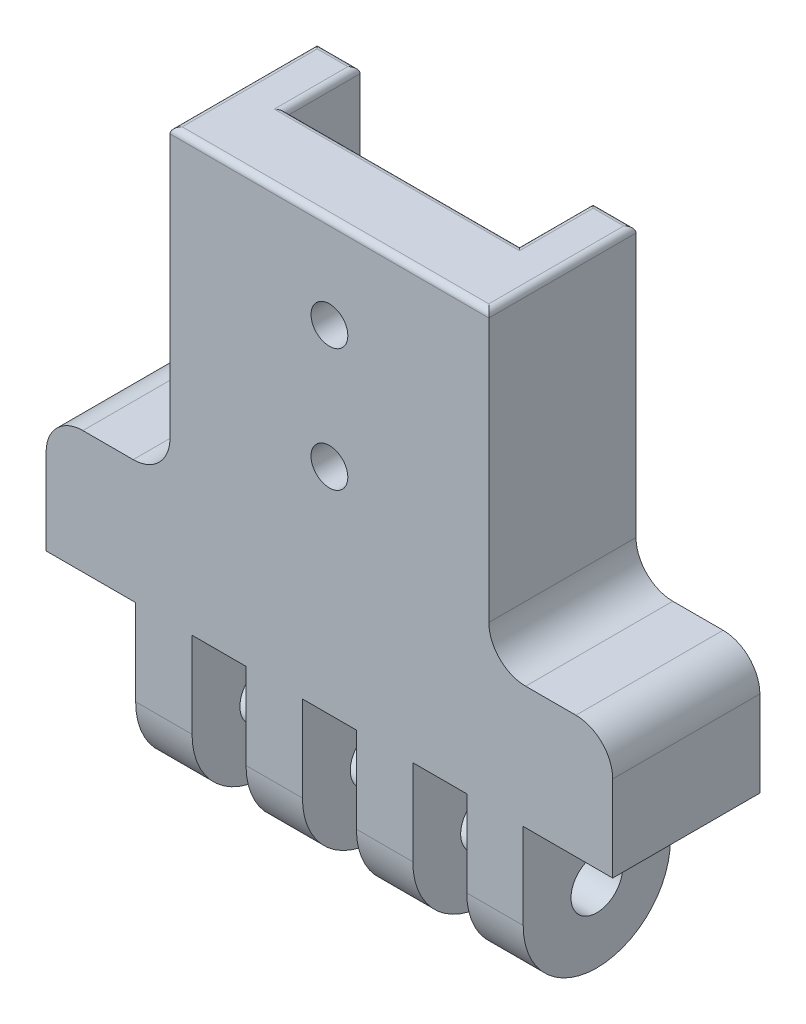
SolidWorks part; units mm, degrees
other "Markup1"
sketch "Sketch9" plane through (-23.1, -13, 8) normal (-0.4776, -0.6311, 0.6112) x (-0.7397, -0.0865, -0.6673)
sketch "Sketch13" plane through (-23.1, -13, 6) normal (-0.4776, -0.6311, 0.6112) x (-0.7397, -0.0865, -0.6673)
ref_plane "Front Plane" through (0, 0, 0) normal (0, 0, 1) x (1, 0, 0)
ref_plane "Top Plane" through (0, 0, 0) normal (0, 1, 0) x (1, 0, 0)
ref_plane "Right Plane" through (0, 0, 0) normal (1, 0, 0) x (0, 0, -1)
sketch "Sketch1" plane through (0, 0, 0) normal (0, 1, 0) x (1, 0, 0)
  line L1 (23.1, 6) -> (-23.1, 6)
  line L2 (23.1, 6) -> (23.1, -6)
  line L3 (23.1, -6) -> (-23.1, -6)
  line L4 (-23.1, 6) -> (-23.1, -6)
  line L5 (23.1, 6) -> (-23.1, -6) construction
  line L6 (23.1, -6) -> (-23.1, 6) construction
  point P0 (0, 0)
  dimension "D1" = 12
  dimension "D2" = 46.2
extrude "Boss-Extrude1" add sketch "Sketch1" along normal blind 10
sketch "Sketch2" plane through (0, 0, 0) normal (0, -1, 0) x (1, 0, 0)
  line L0 (23.1, -6) -> (-23.1, -6) construction
  line L1 (15.8, -6) -> (11.2, -6)
  line L2 (15.8, -6) -> (15.8, 6)
  line L3 (15.8, 6) -> (11.2, 6)
  line L4 (11.2, -6) -> (11.2, 6)
  line L5 (13.5, 8) -> (13.5, -6) construction
  line L6 (15.8, 0) -> (11.2, 0) construction
  point P272 (13.5, 0)
  dimension "D1" = 12
  dimension "D2" = 4.6
extrude "Boss-Extrude2" add sketch "Sketch2" along normal blind 7
sketch "Sketch8" plane through (15.8, 0, 0) normal (1, 0, 0) x (0, 0, -1)
  line L0 (6, -7) -> (-6, -7) construction
  line L1 (6, -7) -> (6, 0) construction
  circle A0 centre (0, -7) radius 6
  dimension "D1" = 12
extrude "Boss-Extrude3" add sketch "Sketch8" against normal up to surface (4.6 mm away) up to face at (11.2, -3.5, 0)
pattern_linear "LPattern1" count 4 spacing 9 along (-1, 0, 0) of "Boss-Extrude2", "Boss-Extrude3"
sketch "Sketch4" plane through (15.8, 0, 0) normal (1, 0, 0) x (0, 0, -1)
  circle A0 centre (0, -7) radius 2.1
  arc A2 (-6, -7) -> (6, -7) centre (0, -7) ccw construction
  dimension "D1" = 4.2
  dimension "D2" = 0
extrude "Cut-Extrude1" cut sketch "Sketch4" against normal through all
ref_plane "Plane1" through (0, 10, 0) normal (0, 1, 0) x (1, 0, 0)
sketch "Sketch10" plane through (0, 10, 0) normal (0, 1, 0) x (1, 0, 0)
  line L0 (23.1, 6) -> (-23.1, 6) construction
  line L1 (13, -6) -> (-13, -6)
  line L2 (13, -6) -> (13, 6)
  line L3 (13, 6) -> (-13, 6)
  line L4 (-13, -6) -> (-13, 6)
  line L5 (13, -6) -> (-13, 6) construction
  line L6 (13, 6) -> (-13, -6) construction
  point P0 (0, 0)
  dimension "D1" = 26
extrude "Boss-Extrude4" add sketch "Sketch10" along normal blind 25
ref_plane "Plane2" through (0, 35, 0) normal (0, 1, 0) x (1, 0, 0)
sketch "Sketch11" plane through (0, 35, 0) normal (0, 1, 0) x (1, 0, 0)
  line L0 (13, 6) -> (-13, 6) construction
  line L1 (9.5, 0) -> (-9.5, 0)
  line L2 (9.5, 0) -> (9.5, 6)
  line L3 (9.5, 6) -> (-9.5, 6)
  line L4 (-9.5, 0) -> (-9.5, 6)
  line L5 (9.5, 0) -> (-9.5, 6) construction
  line L6 (9.5, 6) -> (-9.5, 0) construction
  line L7 (-13, 6) -> (-13, -6) construction
  point P0 (0, 3)
  point P7 (-9.5, 3)
  dimension "D1" = 19
  dimension "D2" = 6
  dimension "D3" = 13
extrude "Cut-Extrude2" cut sketch "Sketch11" against normal blind 25
fillet "Fillet1" radius 3 4 edges at (-13, 10, 0) (13, 10, 0) (23.1, 10, 0) (-23.1, 10, 0)
fillet "Fillet2" radius 0.5 8 edges at (-13, 35, 0) (-11.25, 35, -6) (-9.5, 35, -3) (0, 35, 0) (9.5, 35, -3) (11.25, 35, -6) (13, 35, 0) (0, 35, 6)
sketch "Sketch12" plane through (0, 0, 0) normal (0, 0, 1) x (1, 0, 0)
  line L0 (-18.4905, 22.5) -> (19.9775, 22.5) construction
  line L1 (-20.1, 10) -> (-16, 10) construction
  line L2 (13, 34.5) -> (13, 13) construction
  circle A0 centre (0, 17.5) radius 1.5
  circle A1 centre (0, 27.5) radius 1.5
  dimension "D1" = 3
  dimension "D2" = 10
  dimension "D3" = 5
  dimension "D4" = 12.5
  dimension "D5" = 13
extrude "Cut-Extrude3" cut sketch "Sketch12" against normal mid plane 20
